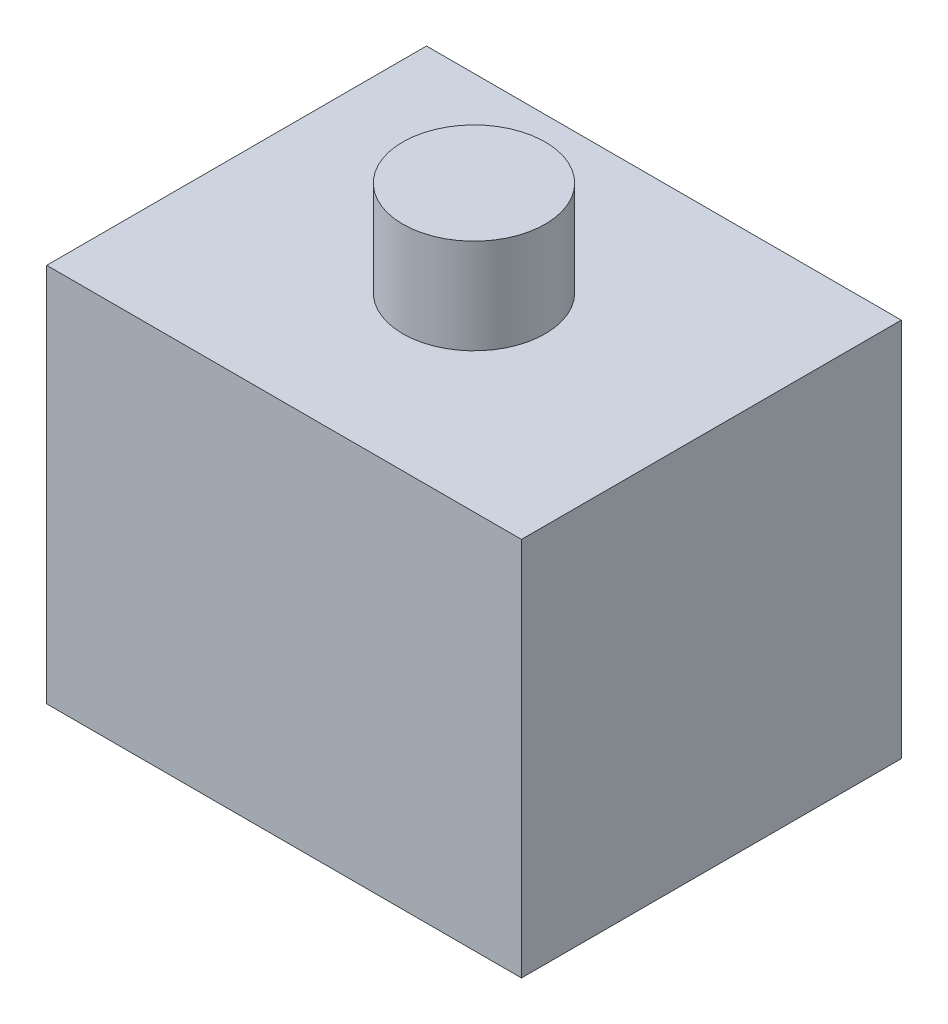
SolidWorks part; units mm, degrees
ref_plane "前视基准面" through (0, 0, 0) normal (0, 0, 1) x (1, 0, 0)
ref_plane "上视基准面" through (0, 0, 0) normal (0, 1, 0) x (1, 0, 0)
ref_plane "右视基准面" through (0, 0, 0) normal (1, 0, 0) x (0, 0, -1)
sketch "草图1" plane through (0, 0, 0) normal (0, 1, 0) x (1, 0, 0)
  line L1 (-10, 8) -> (10, 8)
  line L2 (-10, 8) -> (-10, -8)
  line L3 (-10, -8) -> (10, -8)
  line L4 (10, 8) -> (10, -8)
  dimension "D1" = 20
  dimension "D2" = 16
  dimension "D3" = 10
  dimension "D4" = 8
extrude "凸台-拉伸1" add sketch "草图1" along normal mid plane 16
sketch "草图2" plane through (0, 0, -8) normal (0, 0, -1) x (-1, 0, 0)
  circle A0 centre (0, 0) radius 6
extrude "凸台-拉伸2" add sketch "草图2" along normal blind 2
sketch "草图3" plane through (0, -8, 0) normal (0, -1, 0) x (1, 0, 0)
  circle A0 centre (0, 0) radius 4
extrude "凸台-拉伸3" add sketch "草图3" along normal blind 4
sketch "草图4" plane through (0, 8, 0) normal (0, 1, 0) x (1, 0, 0)
  circle A0 centre (0, 0) radius 3
extrude "凸台-拉伸4" add sketch "草图4" along normal blind 4
